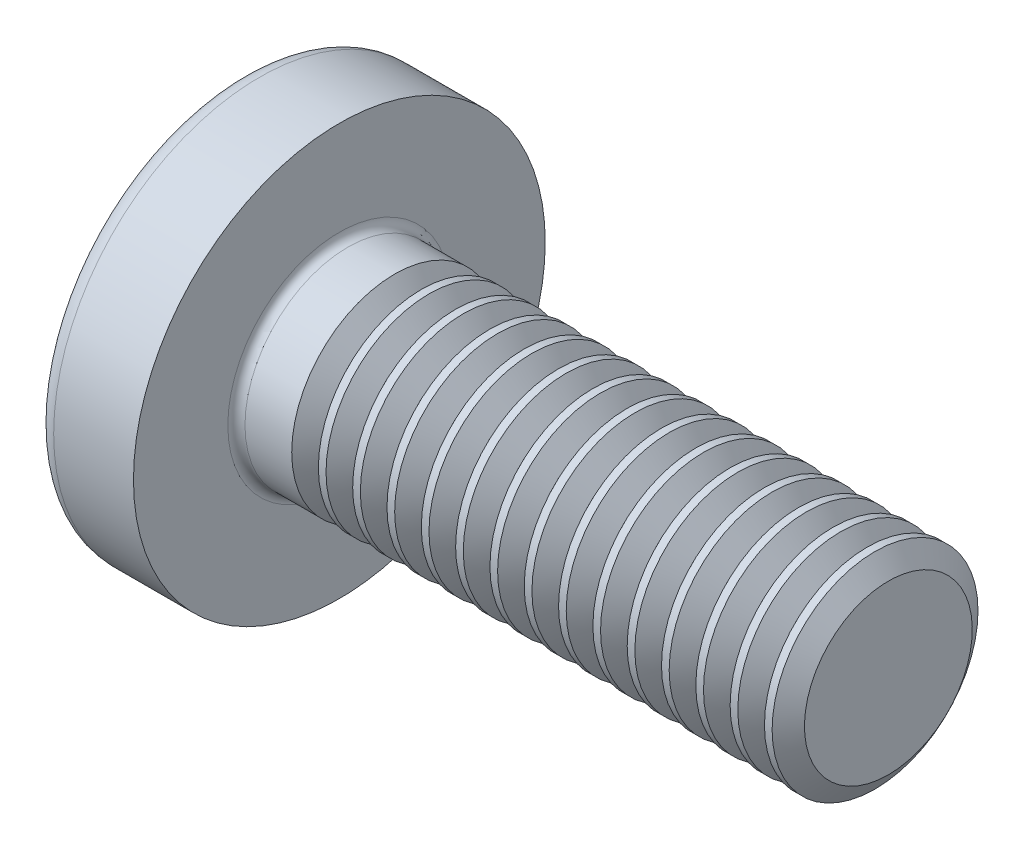
SolidWorks part; units mm, degrees
ref_plane "Plane1" through (0, 0, 0) normal (0, 0, 1) x (1, 0, 0)
ref_plane "Plane2" through (0, 0, 0) normal (0, 1, 0) x (1, 0, 0)
ref_plane "Plane3" through (0, 0, 0) normal (1, 0, 0) x (0, 0, -1)
revolve "Base-Revolve" add sketch "BodySke"
sketch "BodySke" plane through (0, 0, 0) normal (0, 0, 1) x (1, 0, 0)
  line L0 (4.6, 3) -> (4.6, 6)
  line L1 (5.1, 6.35) -> (5.1, -3.175) construction
  line L2 (-25.4, 0) -> (127, 0) construction
  line L3 (20.6, 0) -> (0, 0)
  line L4 (4.6, 3) -> (20.6, 3)
  line L5 (20.6, 3) -> (20.6, 0)
  line L6 (2.2747, 6) -> (4.6, 6)
  line L8 (4.6, 6.35) -> (4.6, -3.175) construction
  arc A0 (1.8337, 5.7717) -> (0, 0) centre (10, 0) ccw
  arc A2 (1.8337, 5.7717) -> (2.2747, 6) centre (2.2747, 5.46) cw
  dimension "Head_fillet_rad" = 0.54
  dimension "Head_crown_rad" = 10
  dimension "Head_ht" = 4.6
  dimension "Diameter" = 6
  dimension "Length" = 16
  dimension "Head_dia" = 12
  dimension "Advance" = 1
  dimension "Thread_nom" = 16
cosmetic thread "ThreadCosmetic" [suppressed]
fillet "Fillet1" radius 0.25 1 edges at (4.6, 0, 3)
sketch "Sketch3" plane through (0, 0, 0) normal (1, 0, 0) x (0, 0, -1)
  line L0 (0.71, -3.35) -> (-0.71, -3.35)
  line L1 (0.71, -3.35) -> (0.71, 3.35)
  line L2 (-0.71, 3.35) -> (0.71, 3.35)
  line L3 (-0.71, 3.35) -> (-0.71, -3.35)
  dimension "D1" = 3.35
  dimension "Cross_dia" = 6.7
  dimension "D2" = 0.71
  dimension "Cross_width" = 1.42
ref_plane "Plane4" through (3.46, 0, 0) normal (1, 0, 0) x (0, 0, -1)
sketch "Sketch4" plane through (3.46, 0, 0) normal (1, 0, 0) x (0, 0, -1)
  line L0 (0.71, -1.6249) -> (-0.71, -1.6249)
  line L1 (0.71, -1.6249) -> (0.71, 1.6249)
  line L2 (-0.71, 1.6249) -> (0.71, 1.6249)
  line L3 (-0.71, 1.6249) -> (-0.71, -1.6249)
  dimension "D1" = 1.42
  dimension "D2" = 3.2498
  dimension "D3" = 0.71
  dimension "D4" = 1.6249
loft "Recess" cut profiles "Sketch3", "Sketch4"
pattern_circular "RecPat" count 2 every 90 about axis through (0, 0, 0) along (1, 0, 0) of "Recess"
sketch "RecCorSke" plane through (0, 0, 0) normal (0, 0, 1) x (1, 0, 0)
  line L0 (-3.175, 0) -> (15.875, 0) construction
  line L1 (-25.4, 0) -> (127, 0) construction
  line L2 (0, 0) -> (0, 1.5224)
  line L3 (0, 1.5224) -> (3.46, 1.2805)
  line L4 (3.46, 1.2805) -> (3.8761, 0)
  line L5 (3.8761, 0) -> (0, 0)
  dimension "Diameter" = 2.561
  dimension "Depth" = 3.46
  dimension "Draft_angle" = 4
  dimension "Bottom_angle" = 18
revolve "RecessCore" cut sketch "RecCorSke" angle 360 about L0
sketch "ThdSchSke" plane through (0, 0, 0) normal (0, 0, 1) x (1, 0, 0)
  line L0 (6.6, -2.4455) -> (6.2117, -3)
  line L1 (6.6, -2.4455) -> (6.9883, -3)
  line L2 (6.9883, -3) -> (6.9883, -3.75)
  line L3 (-3.175, 0) -> (5.1513, 0) construction
  line L5 (6.9883, -3.75) -> (6.2117, -3.75)
  line L6 (6.2117, -3.75) -> (6.2117, -3)
  dimension "Thread_minor" = 4.891
  dimension "Diameter" = 6
  dimension "Start" = 6.6
  dimension "SideAngle" = 55
  dimension "VeeAngle" = 70
  dimension "Overcut" = 7.5
revolve "ThreadSchematic" cut sketch "ThdSchSke" angle 360 about L3
pattern_linear "ThdSchPat" count 15 spacing 1 along (1, 0, 0) of "ThreadSchematic"
equation "\"D1@Sketch3\" = \"Cross_dia@Sketch3\" / 2"
equation "\"D2@Sketch3\" = \"Cross_width@Sketch3\" / 2"
equation "\"Depth@RecCorSke\" = \"Cross_depth@Plane4\""
equation "\"D1@Sketch4\" = \"Cross_width@Sketch3\""
equation "\"D2@Sketch4\" = \"Cross_dia@Sketch3\" - 2.0 * \"Cross_depth@Plane4\" * tan(26.5  * 0.017453292)"
equation "\"D3@Sketch4\" = \"D1@Sketch4\" / 2"
equation "\"D4@Sketch4\" = \"D2@Sketch4\" / 2"
equation "\"Thread_length@ThreadCosmetic\" = ((sgn( (\"Length@BodySke\" - \"Advance@BodySke\" * 2.0 ) - \"Thread_nom@BodySke\" )-1)*( (\"Length@BodySke\" - \"Advance@BodySke\" * 2.0 ) - \"Thread_nom@BodySke\" ))/-2+ \"Thread_nom@BodySke\""
equation "\"Thread_minor@ThdSchSke\" = \"Thread_minor@ThreadCosmetic\""
equation "\"Diameter@ThdSchSke\" = \"Diameter@BodySke\""
equation "\"Overcut@ThdSchSke\" = \"Diameter@BodySke\" * 1.25"
equation "\"Start@ThdSchSke\" = \"Head_ht@BodySke\" + \"Length@BodySke\" - \"Thread_length@ThreadCosmetic\"  '---Non-countersunk---"
equation "\"Num_threads@ThdSchPat\" = int( \"Thread_length@ThreadCosmetic\" / \"Advance@BodySke\" + 0.999 )  + 1"
equation "\"Advance@ThdSchPat\" = \"Thread_length@ThreadCosmetic\" /  (\"Num_threads@ThdSchPat\" - 1) 'relax it"
